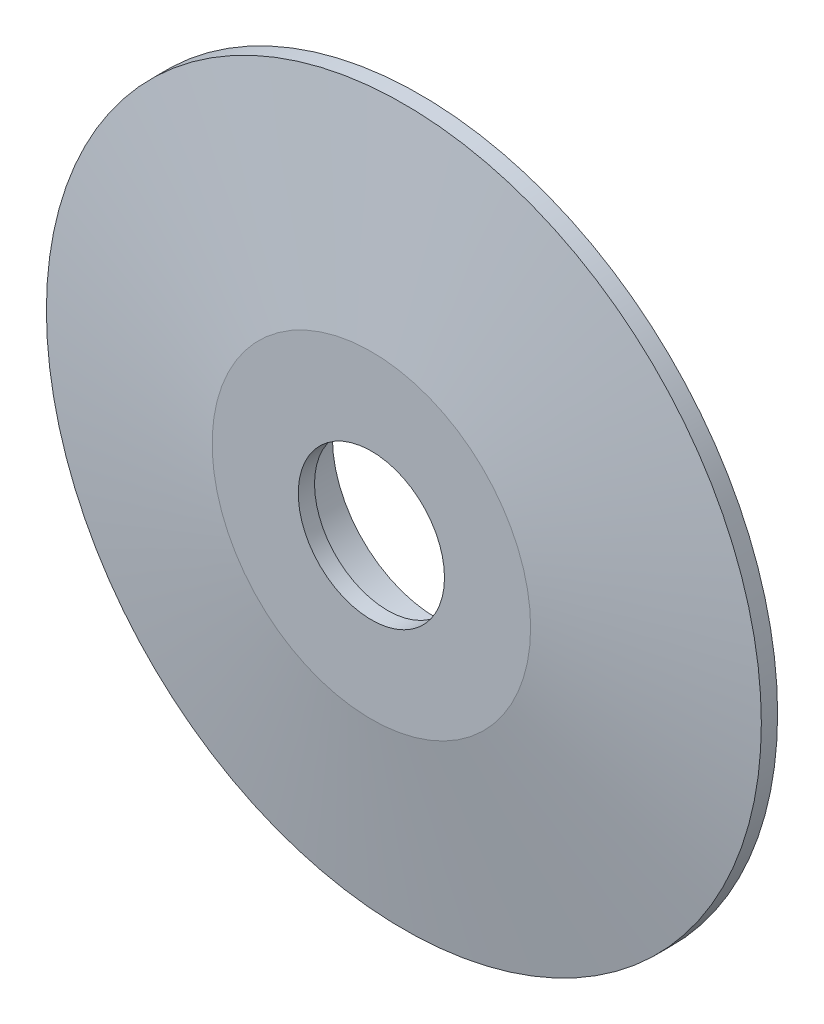
SolidWorks part; units mm, degrees
ref_plane "Front Plane" through (0, 0, 0) normal (0, 0, 1) x (1, 0, 0)
ref_plane "Top Plane" through (0, 0, 0) normal (0, 1, 0) x (1, 0, 0)
ref_plane "Right Plane" through (0, 0, 0) normal (1, 0, 0) x (0, 0, -1)
sketch "Sketch1" plane through (0, 0, 0) normal (0, 0, 1) x (1, 0, 0)
  circle A0 centre (0, 0) radius 22.5
  dimension "D1" = 45
extrude "Boss-Extrude1" add sketch "Sketch1" along normal blind 15
sketch "Sketch2" plane through (0, 0, 0) normal (1, 0, 0) x (0, 0, -1)
  line L0 (-15, 22.5) -> (0, 22.5)
  line L1 (0, 109.5929) -> (0, 110)
  line L2 (0, 110) -> (-5, 110)
  line L3 (-5, 110) -> (-15, 49)
  line L4 (-15, 49) -> (-15, 22.5)
  line L5 (0, 109.5929) -> (-10, 48.5929)
  line L6 (-10, 48.5929) -> (-10, 22.5)
  line L7 (-0.0659, 109.1911) -> (-10, 48.5929) construction
  point P11 (0, 0)
  point P12 (0, 0)
  point P13 (-0.0604, 110)
  dimension "D1" = 110
  dimension "D2" = 5
  dimension "D3" = 49
  dimension "D4" = 5
ref_axis "Axis1" through (0, 0, 15) along (0, 0, -1)
revolve "Revolve1" add sketch "Sketch2" angle 360 about axis through (0, 0, 15) along (0, 0, -1)
sketch "Sketch3" plane through (0, 0, 15) normal (0, 0, 1) x (1, 0, 0)
  circle A0 centre (0, 0) radius 22.5
  dimension "D1" = 45
extrude "Cut-Extrude1" cut sketch "Sketch3" against normal blind 43
sketch "Sketch4" plane through (0, 0, 10) normal (0, 0, -1) x (-1, 0, 0)
  circle A0 centre (0, 0) radius 32
  circle A1 centre (0, 0) radius 37
  dimension "D1" = 64
  dimension "D2" = 74
extrude "Boss-Extrude2" add sketch "Sketch4" along normal blind 15
